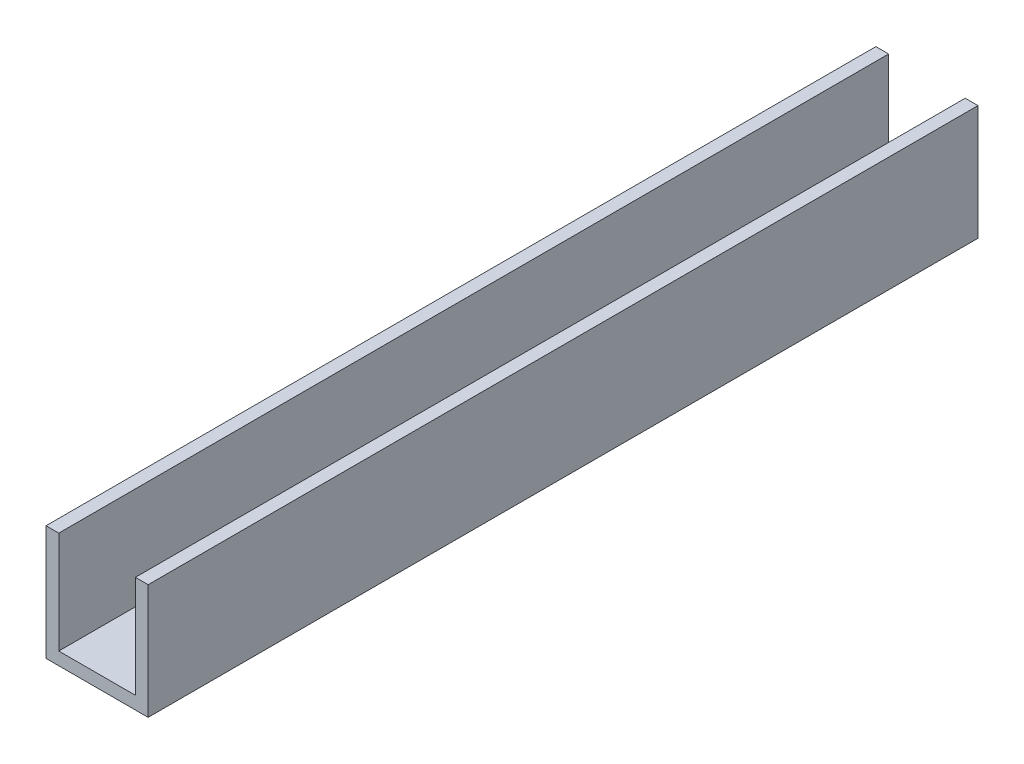
SolidWorks part; units mm, degrees
ref_plane "Alzado" through (0, 0, 0) normal (0, 0, 1) x (1, 0, 0)
ref_plane "Planta" through (0, 0, 0) normal (0, 1, 0) x (1, 0, 0)
ref_plane "Vista lateral" through (0, 0, 0) normal (1, 0, 0) x (0, 0, -1)
sketch "Croquis1" plane through (0, 0, 0) normal (0, 0, 1) x (1, 0, 0)
  line L0 (0, 0) -> (-800, 0)
  line L1 (0, 0) -> (0, 900)
  line L2 (-800, 0) -> (-800, 900)
  line L3 (-700, 100) -> (-100, 100)
  line L4 (-100, 100) -> (-100, 900)
  line L5 (-100, 900) -> (0, 900)
  line L6 (-700, 100) -> (-700, 900)
  line L7 (-700, 900) -> (-800, 900)
  point P11 (-100, 500)
  dimension "D1" = 800
  dimension "D2" = 900
  dimension "D3" = 900
  dimension "D4" = 100
  dimension "D5" = 100
  dimension "D6" = 100
extrude "Saliente-Extruir1" add sketch "Croquis1" along normal blind 6500
